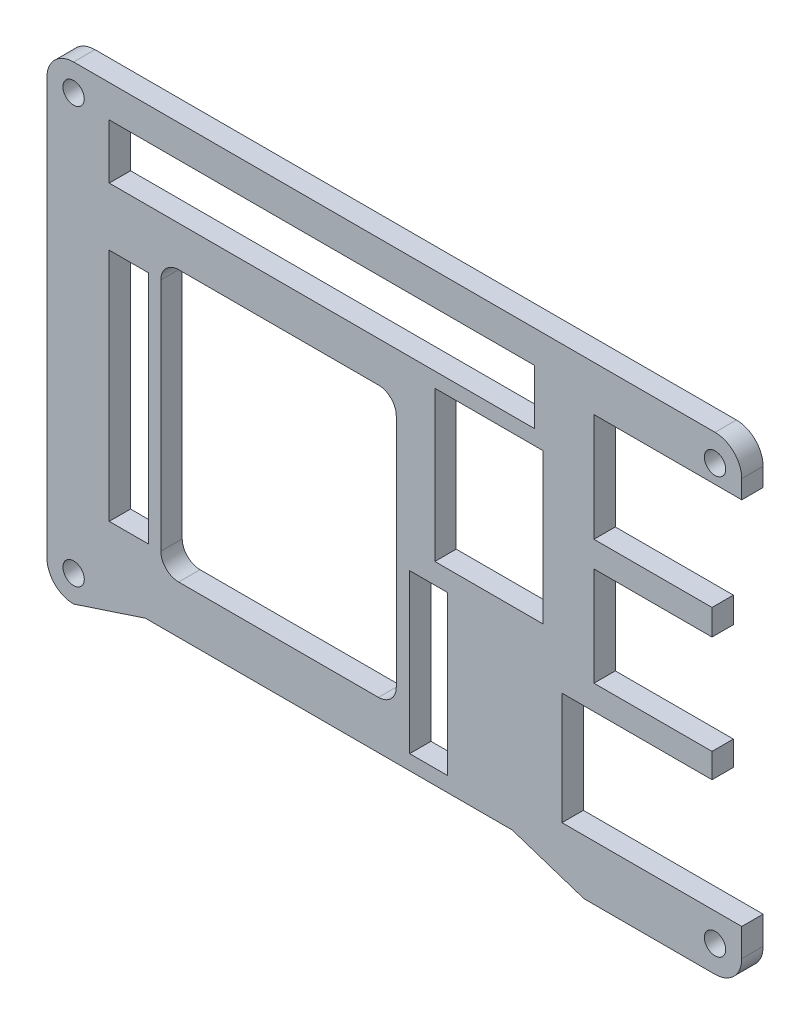
SolidWorks part; units mm, degrees
ref_plane "Front Plane" through (0, 0, 0) normal (0, 0, 1) x (1, 0, 0)
ref_plane "Top Plane" through (0, 0, 0) normal (0, 1, 0) x (1, 0, 0)
ref_plane "Right Plane" through (0, 0, 0) normal (1, 0, 0) x (0, 0, -1)
sketch "Sketch1" plane through (0, 0, 0) normal (0, 0, 1) x (1, 0, 0)
  line L3 (56.975, 4.9979) -> (56.975, 8.6582) construction
  line L7 (56.975, -12.628) -> (56.975, -9.1218) construction
  line L8 (35.575, -12.628) -> (56.975, -12.628) construction
  line L9 (35.575, -28.6278) -> (35.575, -12.628) construction
  line L10 (61.2149, -28.6278) -> (35.575, -28.6278) construction
  line L11 (61.2149, -32.6134) -> (61.2149, -28.6278) construction
  line L12 (38.7143, -36.451) -> (57.405, -36.451) construction
  line L13 (28.4743, -33.0844) -> (38.7143, -36.451) construction
  line L14 (61.2149, 24.0683) -> (61.2149, 26.6839) construction
  line L15 (61.2149, 24.0683) -> (40.1348, 24.0683)
  line L16 (40.1348, 24.0683) -> (40.1348, 8.6582)
  line L17 (40.1348, 8.6582) -> (56.975, 8.6582)
  line L18 (56.975, 4.9979) -> (56.975, 8.6582)
  line L19 (56.975, 4.9979) -> (40.1348, 4.9979)
  line L20 (40.1348, 4.9979) -> (40.1348, -9.1218)
  line L21 (40.1348, -9.1218) -> (56.975, -9.1218)
  line L22 (56.975, -12.628) -> (56.975, -9.1218)
  line L23 (35.575, -12.628) -> (56.975, -12.628)
  line L24 (35.575, -28.6278) -> (35.575, -12.628)
  line L25 (61.2149, -28.6278) -> (35.575, -28.6278)
  line L26 (61.2149, -32.6134) -> (61.2149, -28.6278)
  line L27 (38.7143, -36.451) -> (57.405, -36.451)
  line L28 (28.4743, -33.0844) -> (38.7143, -36.451)
  line L29 (61.2149, 24.0683) -> (61.2149, 26.6839)
  line L30 (57.4049, 30.5077) -> (-34.0849, 30.5077) construction
  line L31 (-37.8949, 26.6977) -> (-37.8949, -32.641) construction
  line L32 (-34.0849, -36.451) -> (-23.8449, -33.0844) construction
  line L33 (57.4049, 30.5077) -> (-34.0849, 30.5077)
  line L34 (-37.8949, 26.6977) -> (-37.8949, -32.641)
  line L35 (-34.0849, -36.451) -> (-23.8449, -33.0844)
  line L36 (-23.8449, -33.0844) -> (28.4743, -33.0844)
  line L40 (13.845, -30.9668) -> (13.845, -8.3602)
  line L41 (13.845, -8.3602) -> (19.2484, -8.3602)
  line L42 (19.2484, -8.3602) -> (19.2484, -30.9668)
  line L43 (19.2484, -30.9668) -> (13.845, -30.9668)
  line L45 (-29.0049, 25.897) -> (31.6883, 25.897)
  line L46 (-29.0049, 25.897) -> (-29.0049, 18.087)
  line L47 (-29.0049, 18.087) -> (31.6883, 18.087)
  line L48 (31.6883, 25.897) -> (31.6883, 18.087)
  line L49 (17.441, 15.9724) -> (32.872, 15.9724)
  line L50 (17.441, 15.9724) -> (17.441, -5.4315)
  line L51 (17.441, -5.4315) -> (32.872, -5.4315)
  line L52 (32.872, 15.9724) -> (32.872, -5.4315)
  line L53 (-21.6389, 10.5941) -> (10.329, 10.5941)
  line L54 (-21.6389, 10.5941) -> (-21.6389, -7.643)
  line L55 (-21.6389, -7.643) -> (10.329, -7.643)
  line L56 (10.329, 10.5941) -> (10.329, -7.643)
  line L57 (-23.4169, 9.8012) -> (-29.0049, 9.8012)
  line L58 (-23.4169, 9.8012) -> (-23.4169, -23.6989)
  line L59 (-23.4169, -23.6989) -> (-29.0049, -23.6989)
  line L60 (-29.0049, 9.8012) -> (-29.0049, -23.6989)
  arc A0 (57.405, -36.451) -> (61.2149, -32.6134) centre (57.405, -32.641) ccw construction
  arc A1 (61.2149, 26.6839) -> (57.4049, 30.5077) centre (57.4049, 26.6977) ccw construction
  circle A2 centre (57.4049, 26.6977) radius 1.3462 construction
  circle A3 centre (57.405, -32.641) radius 1.3462 construction
  circle A4 centre (-34.0849, -32.641) radius 1.3462 construction
  circle A5 centre (-34.0849, 26.6977) radius 1.3462 construction
  arc A6 (57.405, -36.451) -> (61.2149, -32.6134) centre (57.405, -32.641) ccw
  arc A7 (61.2149, 26.6839) -> (57.4049, 30.5077) centre (57.4049, 26.6977) ccw
  circle A8 centre (57.4049, 26.6977) radius 1.3462
  circle A9 centre (57.405, -32.641) radius 1.3462
  circle A10 centre (-34.0849, -32.641) radius 1.3462
  circle A11 centre (-34.0849, 26.6977) radius 1.3462
  arc A12 (-34.0849, 30.5077) -> (-37.8949, 26.6977) centre (-34.0849, 26.6977) ccw construction
  arc A13 (-37.8949, -32.641) -> (-34.0849, -36.451) centre (-34.0849, -32.641) ccw construction
  arc A14 (-34.0849, 30.5077) -> (-37.8949, 26.6977) centre (-34.0849, 26.6977) ccw
  arc A15 (-37.8949, -32.641) -> (-34.0849, -36.451) centre (-34.0849, -32.641) ccw
  dimension "D1" = 16.8402
  dimension "D2" = 16.8402
extrude "Boss-Extrude1" add sketch "Sketch1" along normal blind 3.048
sketch "Sketch2" plane through (0, 0, 3.048) normal (0, 0, 1) x (1, 0, 0)
  line L0 (-21.6389, 10.5941) -> (-21.6389, -7.643) construction
  line L1 (11.94, 12.3412) -> (-21.6389, 12.3412)
  line L2 (11.94, 12.3412) -> (11.94, -26.2389)
  line L3 (11.94, -26.2389) -> (-21.6389, -26.2389)
  line L4 (-21.6389, 12.3412) -> (-21.6389, -26.2389)
  line L6 (-23.4169, 9.8012) -> (-29.0049, 9.8012) construction
  line L9 (-29.0049, -23.6989) -> (-23.4169, -23.6989) construction
  line L10 (13.845, -8.3602) -> (13.845, -30.9668) construction
  dimension "D1" = 2.54
  dimension "D2" = 2.54
  dimension "D3" = 1.905
extrude "Cut-Extrude1" cut sketch "Sketch2" against normal through all
fillet "Fillet1" radius 2.54 4 edges at (11.94, -26.2389, 1.524) (-21.6389, -26.2389, 1.524) (-21.6389, 12.3412, 1.524) (11.94, 12.3412, 1.524)
sketch "Sketch3" plane through (0, 0, 3.048) normal (0, 0, 1) x (1, 0, 0)
  circle A0 centre (-34.0849, 26.6977) radius 1.524
  circle A1 centre (57.4049, 26.6977) radius 1.524
  circle A2 centre (57.405, -32.641) radius 1.524
  circle A3 centre (-34.0849, -32.641) radius 1.524
  dimension "D1" = 3.048
extrude "Cut-Extrude2" cut sketch "Sketch3" against normal through all
